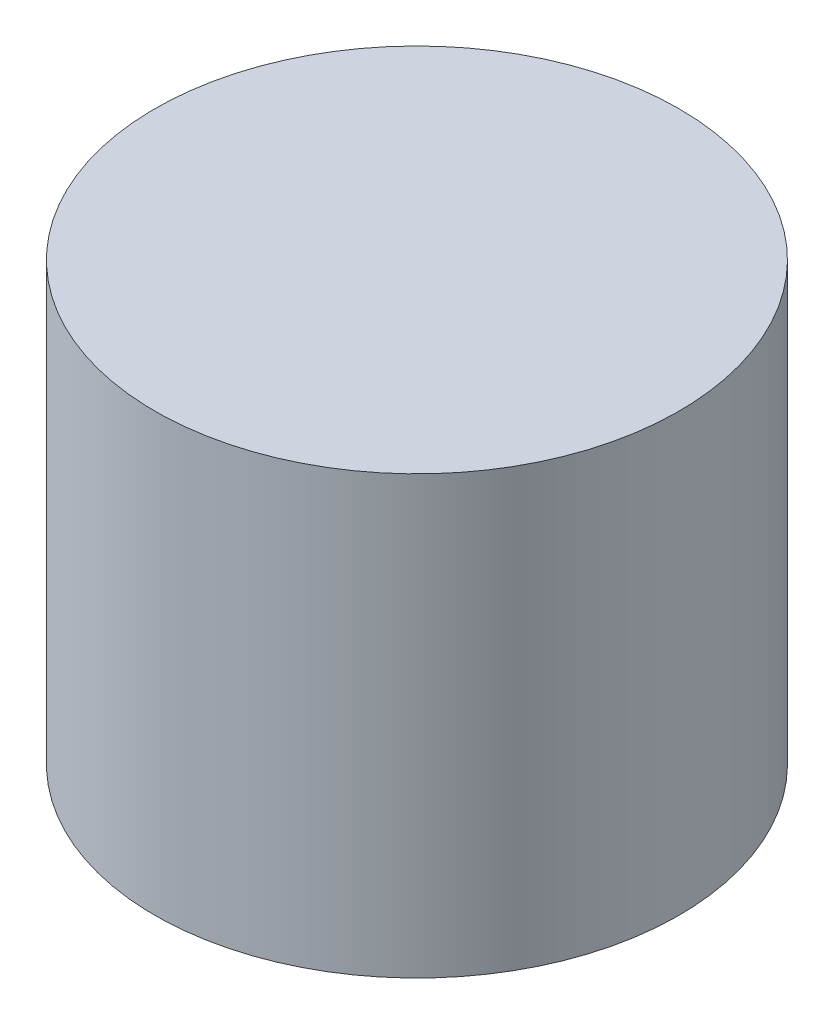
SolidWorks part; units mm, degrees
ref_plane "Спереди" through (0, 0, 0) normal (0, 0, 1) x (1, 0, 0)
ref_plane "Сверху" through (0, 0, 0) normal (0, 1, 0) x (1, 0, 0)
ref_plane "Справа" through (0, 0, 0) normal (1, 0, 0) x (0, 0, -1)
sketch "Эскиз1" plane through (0, 0, 0) normal (0, 0, 1) x (1, 0, 0)
  line L1 (0, 0) -> (90, 0)
  line L2 (0, 0) -> (0, 150)
  line L3 (0, 150) -> (90, 150)
  line L4 (90, 0) -> (90, 150)
  dimension "D1" = 90
  dimension "D2" = 150
revolve "Повернуть1" add sketch "Эскиз1" angle 360 about L2
sketch "Эскиз2" plane through (0, 0, 0) normal (0, -1, 0) x (1, 0, 0)
  circle A0 centre (0, 0) radius 70
  dimension "D1" = 140
sketch "Эскиз3" plane through (0, 0, 0) normal (1, 0, 0) x (0, 0, -1)
  line L0 (0, 0) -> (0, 70)
  line L1 (0, 0) -> (70, 0)
  arc A0 (70, 0) -> (0, 70) centre (0, 0) ccw
  dimension "D1" = 70
revolve "Вырез-Повернуть1" cut sketch "Эскиз3" angle 360 about L0
